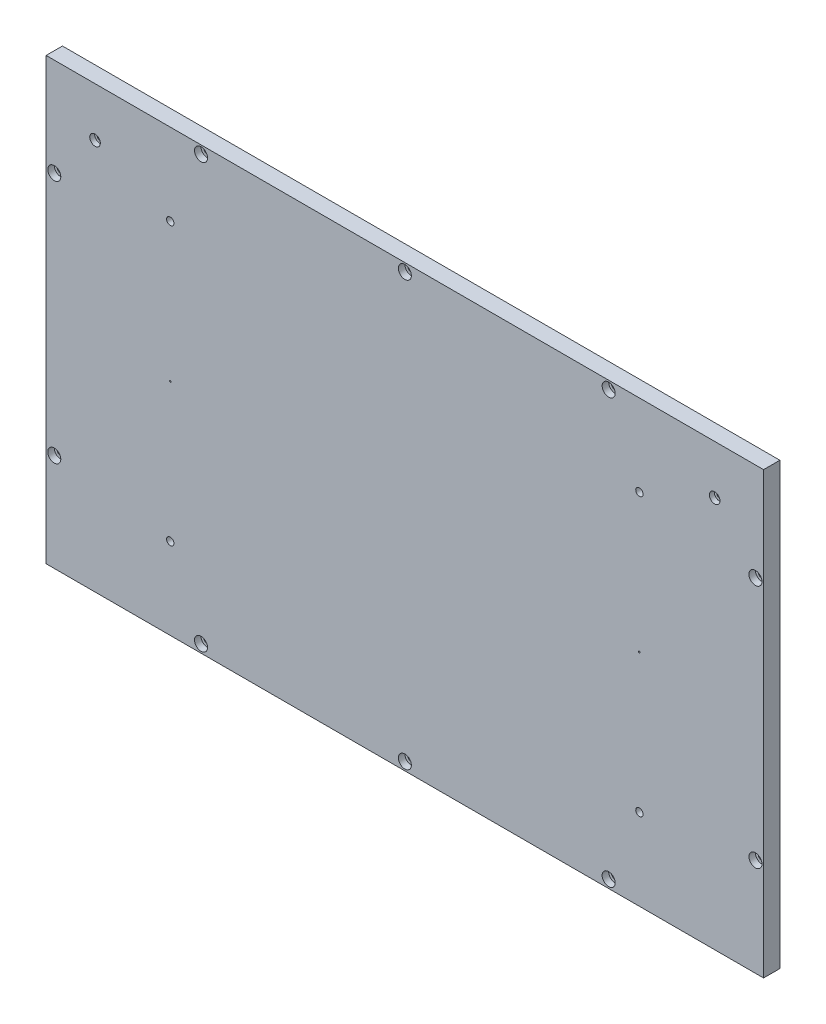
SolidWorks part; units mm, degrees
ref_plane "Front Plane" through (0, 0, 0) normal (0, 0, 1) x (1, 0, 0)
ref_plane "Top Plane" through (0, 0, 0) normal (0, 1, 0) x (1, 0, 0)
ref_plane "Right Plane" through (0, 0, 0) normal (1, 0, 0) x (0, 0, -1)
sketch "Sketch1" plane through (0, 0, 0) normal (0, 0, 1) x (1, 0, 0)
  line L0 (0, -55) -> (0, 55) construction
  line L1 (-30, -30) -> (410, -30)
  line L2 (-30, -30) -> (-30, 240)
  line L3 (-30, 240) -> (410, 240)
  line L4 (410, -30) -> (410, 240)
  line L5 (55, 0) -> (-55, 0) construction
  dimension "D1" = 30
  dimension "D2" = 30
  dimension "D3" = 440
  dimension "D4" = 270
extrude "Boss-Extrude1" add sketch "Sketch1" against normal blind 10
ref_plane "Mid X Plane" through (190, 0, 0) normal (-1, 0, 0) x (0, 0, 1)
ref_plane "Mid Y Plane" through (0, 105, 0) normal (0, -1, 0) x (-1, 0, 0)
hole_wizard "CBORE for M4 SHCS3" positions "Sketch6" profile "Sketch7" counterbore size "M4" standard "ANSI Metric"
sketch "Sketch6" plane through (0, 0, -10) normal (0, 0, -1) x (-1, 0, 0)
  line L0 (-190, -5.5) -> (-190, 5.5) construction
  line L1 (-5.5, 105) -> (5.5, 105) construction
  point P0 (-46.15, 20)
  dimension "D1" = 143.85
  dimension "D2" = 85
sketch "Sketch7" plane through (46.15, 20, -10) normal (1, 0, 0) x (0, 1, 0)
  line L0 (0, 0) -> (0, 12.8519)
  line L1 (0, 12.8519) -> (2.25, 11.5)
  line L2 (2.25, 11.5) -> (2.25, 4)
  line L3 (2.25, 4) -> (4, 4)
  line L4 (4, 4) -> (4, 0)
  line L5 (4, 0) -> (0, 0)
  line L10 (0, 12.8519) -> (-2.25, 11.5) construction
  line L11 (0, -6.35) -> (0, 107.95) construction
  dimension "Hole Dia." = 4.5
  dimension "Hole Depth" = 11.5
  dimension "C'Bore Dia." = 8
  dimension "C'Bore Depth" = 4
  dimension "Drill Angle" = 118
mirror "Mirror1" about plane through (0, 105, 0) normal (0, -1, 0) of "CBORE for M4 SHCS3"
mirror "Mirror2" about plane through (190, 0, 0) normal (-1, 0, 0) of "Mirror1", "CBORE for M4 SHCS3"
hole_wizard "CBORE for M4 SHCS4" positions "Sketch8" profile "Sketch9" counterbore size "M4" standard "ANSI Metric"
sketch "Sketch8" plane through (0, 0, 0) normal (0, 0, 1) x (1, 0, 0)
  line L0 (190, 5.5) -> (190, -5.5) construction
  line L1 (410, 240) -> (-30, 240) construction
  line L2 (-30, -30) -> (410, -30) construction
  line L3 (-30, 240) -> (-30, -30) construction
  line L4 (410, -30) -> (410, 240) construction
  line L5 (-5.5, 105) -> (5.5, 105) construction
  point P0 (65, 235)
  point P2 (190, 235)
  point P4 (315, 235)
  point P6 (315, -25)
  point P8 (190, -25)
  point P10 (65, -25)
  point P12 (405, 180)
  point P14 (405, 30)
  point P16 (-25, 30)
  point P18 (-25, 180)
  dimension "D1" = 125
  dimension "D2" = 125
  dimension "D3" = 5
  dimension "D4" = 5
  dimension "D5" = 5
  dimension "D6" = 5
  dimension "D7" = 75
  dimension "D8" = 75
sketch "Sketch9" plane through (65, 235, 0) normal (1, 0, 0) x (0, -1, 0)
  line L0 (0, 0) -> (0, 12.8519)
  line L1 (0, 12.8519) -> (2.25, 11.5)
  line L2 (2.25, 11.5) -> (2.25, 4)
  line L3 (2.25, 4) -> (4, 4)
  line L4 (4, 4) -> (4, 0)
  line L5 (4, 0) -> (0, 0)
  line L10 (0, 12.8519) -> (-2.25, 11.5) construction
  line L11 (0, -6.35) -> (0, 107.95) construction
  dimension "Hole Dia." = 4.5
  dimension "Hole Depth" = 11.5
  dimension "C'Bore Dia." = 8
  dimension "C'Bore Depth" = 4
  dimension "Drill Angle" = 118
hole_wizard "Ø1.0mm Dowel Hole1" positions "Sketch10" profile "Sketch11" hole size "Ø1.0" standard "ANSI Metric"
sketch "Sketch10" plane through (0, 0, 0) normal (0, 0, 1) x (1, 0, 0)
  line L0 (-5.5, 105) -> (5.5, 105) construction
  line L1 (190, 5.5) -> (190, -5.5) construction
  point P0 (46.15, 105)
  dimension "D1" = 143.85
sketch "Sketch11" plane through (46.15, 105, 0) normal (1, 0, 0) x (0, -1, 0)
  line L0 (0, 0) -> (0, 5.3004)
  line L1 (0, 5.3004) -> (0.5, 5)
  line L2 (0.5, 5) -> (0.5, 0)
  line L5 (0.5, 0) -> (0, 0)
  line L10 (0, 5.3004) -> (-0.5, 5) construction
  line L11 (0, -6.35) -> (0, 107.95) construction
  dimension "Hole Dia." = 1
  dimension "Hole Depth" = 5
  dimension "Drill Angle" = 118
mirror "Mirror3" about plane through (190, 0, 0) normal (-1, 0, 0) of "Ø1.0mm Dowel Hole1"
hole_wizard "CBORE for M3 SHCS1" positions "Sketch12" profile "Sketch13" counterbore size "M3" standard "ANSI Metric" end condition through all
sketch "Sketch12" plane through (0, 0, 0) normal (0, 0, 1) x (1, 0, 0)
  line L0 (-5.5, 105) -> (5.5, 105) construction
  point P0 (0, 210)
  dimension "D1" = 105
sketch "Sketch13" plane through (0, 210, 0) normal (1, 0, 0) x (0, -1, 0)
  line L0 (0, 0) -> (0, 10)
  line L1 (0, 10) -> (1.7, 10)
  line L3 (1.7, 10) -> (1.7, 3)
  line L4 (1.7, 3) -> (3.25, 3)
  line L5 (3.25, 3) -> (3.25, 0)
  line L7 (3.25, 0) -> (0, 0)
  line L11 (0, -6.35) -> (0, 107.95) construction
  dimension "Thru Hole Dia." = 3.4
  dimension "Thru Hole Depth" = 10
  dimension "C'Bore Dia." = 6.5
  dimension "C'Bore Depth" = 3
mirror "Mirror4" about plane through (190, 0, 0) normal (-1, 0, 0) of "CBORE for M3 SHCS1"
